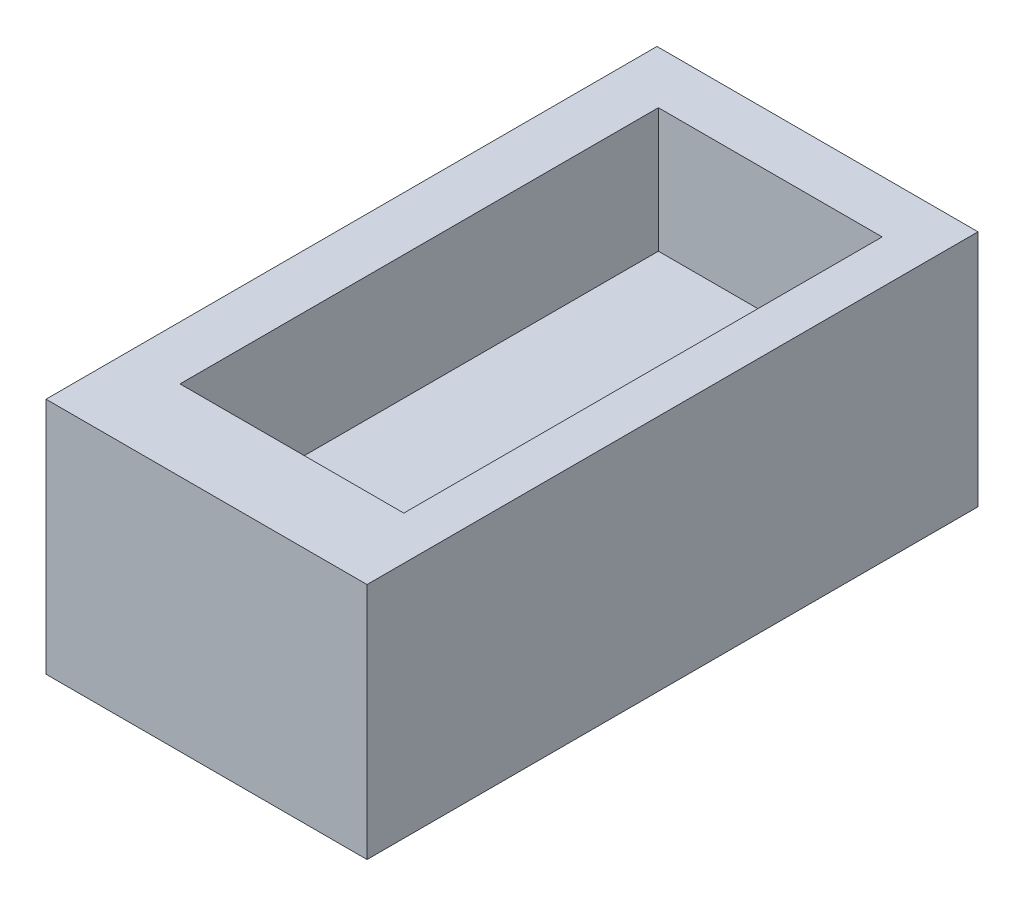
SolidWorks part; units mm, degrees
material "6061-T6 (SS)"
ref_plane "Front Plane" through (0, 0, 0) normal (0, 0, 1) x (1, 0, 0)
ref_plane "Top Plane" through (0, 0, 0) normal (0, 1, 0) x (1, 0, 0)
ref_plane "Right Plane" through (0, 0, 0) normal (1, 0, 0) x (0, 0, -1)
sketch "Sketch1" plane through (0, 0, 0) normal (0, 1, 0) x (1, 0, 0)
  line L1 (15.5, -29.5) -> (-15.5, -29.5)
  line L2 (15.5, -29.5) -> (15.5, 29.5)
  line L3 (15.5, 29.5) -> (-15.5, 29.5)
  line L4 (-15.5, -29.5) -> (-15.5, 29.5)
  line L5 (15.5, -29.5) -> (-15.5, 29.5) construction
  line L6 (15.5, 29.5) -> (-15.5, -29.5) construction
  point P0 (0, 0)
  dimension "D1" = 31
  dimension "D2" = 59
extrude "Boss-Extrude1" add sketch "Sketch1" along normal blind 23
sketch "Sketch2" plane through (0, 23, 0) normal (0, 1, 0) x (1, 0, 0)
  line L1 (-10.3075, 24.4444) -> (11.3017, 24.4444)
  line L2 (-10.3075, 24.4444) -> (-10.3075, -21.7499)
  line L3 (-10.3075, -21.7499) -> (11.3017, -21.7499)
  line L4 (11.3017, 24.4444) -> (11.3017, -21.7499)
extrude "Cut-Extrude1" cut sketch "Sketch2" against normal blind 12
